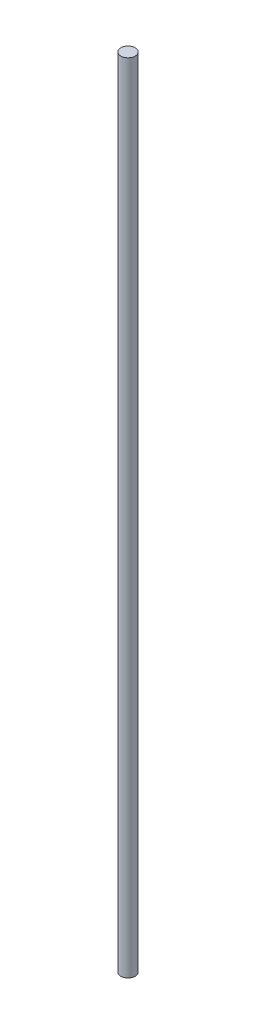
SolidWorks part; units mm, degrees
material "1060 Alloy"
ref_plane "Front Plane" through (0, 0, 0) normal (0, 0, 1) x (1, 0, 0)
ref_plane "Top Plane" through (0, 0, 0) normal (0, 1, 0) x (1, 0, 0)
ref_plane "Right Plane" through (0, 0, 0) normal (1, 0, 0) x (0, 0, -1)
sketch "Sketch1" plane through (0, 0, 0) normal (0, 1, 0) x (1, 0, 0)
  circle A0 centre (0, 0) radius 3.175
  dimension "D1" = 6.35
extrude "Boss-Extrude1" add sketch "Sketch1" along normal blind 350
